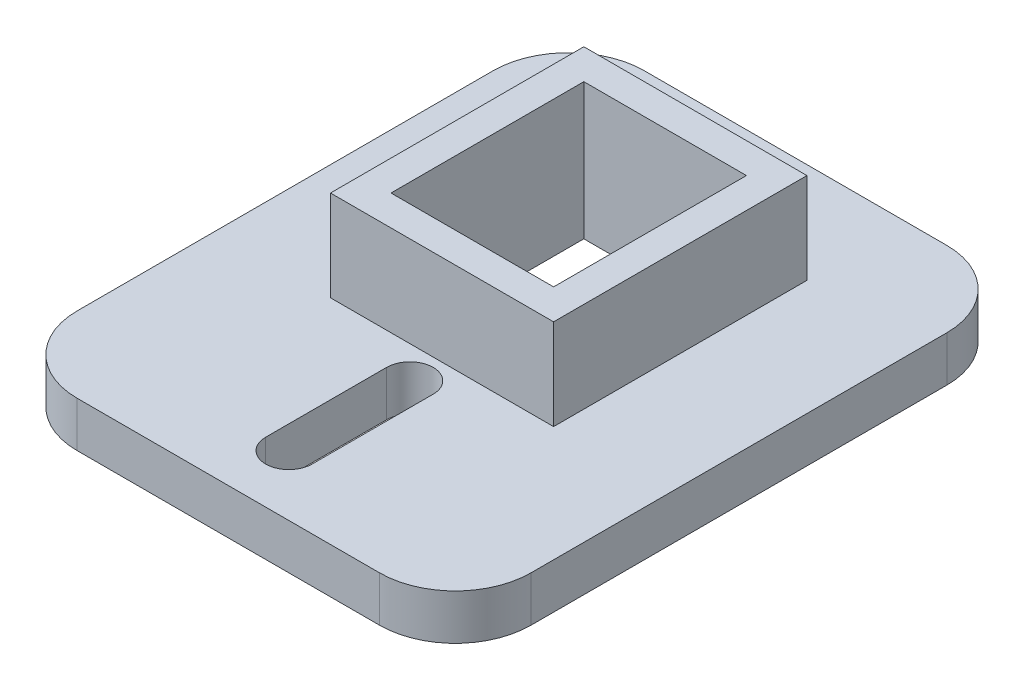
SolidWorks part; units mm, degrees
ref_plane "Front Plane" through (0, 0, 0) normal (0, 0, 1) x (1, 0, 0)
ref_plane "Top Plane" through (0, 0, 0) normal (0, 1, 0) x (1, 0, 0)
ref_plane "Right Plane" through (0, 0, 0) normal (1, 0, 0) x (0, 0, -1)
sketch "Sketch1" plane through (0, 0, 0) normal (0, 1, 0) x (1, 0, 0)
  line L0 (0, 14.375) -> (0, -23.125) construction
  line L1 (-15, -23.125) -> (15, -23.125)
  line L2 (-15, -23.125) -> (-15, 14.375)
  line L3 (-15, 14.375) -> (15, 14.375)
  line L4 (15, -23.125) -> (15, 14.375)
  line L5 (0, -11.125) -> (0, -19.125) construction
  line L6 (1.5375, -11.125) -> (1.5375, -19.125)
  line L7 (-1.5375, -11.125) -> (-1.5375, -19.125)
  line L8 (-5.375, -7) -> (5.375, -7)
  line L9 (-5.375, -7) -> (-5.375, 5.75)
  line L10 (-5.375, 5.75) -> (5.375, 5.75)
  line L11 (5.375, -7) -> (5.375, 5.75)
  line L12 (-5.375, -7) -> (5.375, 5.75) construction
  line L13 (-5.375, 5.75) -> (5.375, -7) construction
  arc A0 (1.5375, -11.125) -> (-1.5375, -11.125) centre (0, -11.125) ccw
  arc A1 (-1.5375, -19.125) -> (1.5375, -19.125) centre (0, -19.125) ccw
  point P0 (0, 0)
  point P8 (0, -0.625)
  point P15 (0, -15.125)
  dimension "D6" = 1.5375
  dimension "D1" = 10.75
  dimension "D2" = 12.75
  dimension "D3" = 15
  dimension "D4" = 22.5
  dimension "D5" = 30
  dimension "D7" = 8
  dimension "D8" = 4
extrude "Boss-Extrude1" add sketch "Sketch1" along normal blind 3
fillet "Fillet1" radius 5 4 edges at (15, 1.5, 23.125) (-15, 1.5, 23.125) (15, 1.5, -14.375) (-15, 1.5, -14.375)
sketch "Sketch2" plane through (0, 3, 0) normal (0, 1, 0) x (1, 0, 0)
  line L0 (-7.375, 7.75) -> (-7.375, -9)
  line L1 (-5.375, 5.75) -> (5.375, 5.75)
  line L2 (-5.375, 5.75) -> (-5.375, -7)
  line L3 (-5.375, -7) -> (5.375, -7)
  line L4 (5.375, 5.75) -> (5.375, -7)
  line L5 (-7.375, -9) -> (7.375, -9)
  line L6 (7.375, 7.75) -> (7.375, -9)
  line L7 (-7.375, 7.75) -> (7.375, 7.75)
  dimension "D1" = 2
extrude "Boss-Extrude2" add sketch "Sketch2" along normal blind 6
